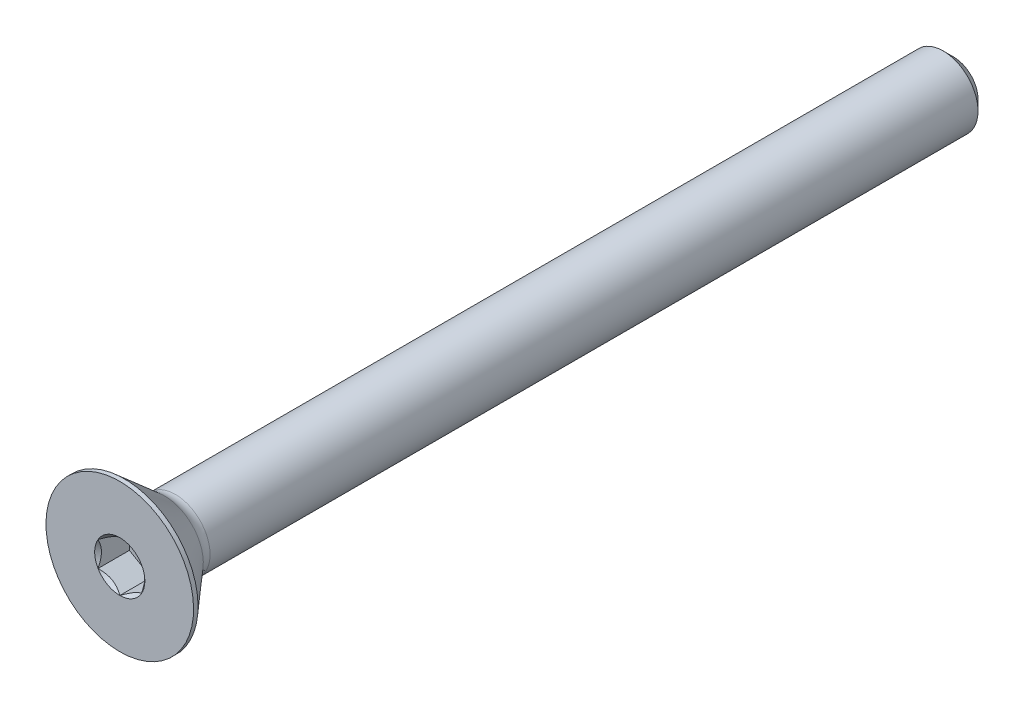
SolidWorks part; units mm, degrees
ref_plane "Front" through (0, 0, 0) normal (0, 0, 1) x (1, 0, 0)
ref_plane "Top" through (0, 0, 0) normal (0, 1, 0) x (1, 0, 0)
ref_plane "Right" through (0, 0, 0) normal (1, 0, 0) x (0, 0, -1)
sketch "Sketch1" plane through (0, 0, 0) normal (1, 0, 0) x (0, 0, -1)
  line L0 (0, 6.7437) -> (0.4089, 6.7437) construction
  line L1 (0.4089, 6.7437) -> (4.0894, 3.5443) construction
  line L2 (0, 3.175) -> (76.2, 3.175)
  line L3 (76.2, 3.175) -> (76.2, 0)
  line L4 (76.2, 0) -> (0, 0)
  line L5 (0, 0) -> (0, 6.7437) construction
  line L6 (0, 6.7437) -> (0, -6.7437) construction
  line L7 (76.2, 3.175) -> (76.2, -3.175) construction
  line L8 (0, -6.7437) -> (0.4089, -6.7437) construction
  line L9 (0.4089, -6.7437) -> (4.0894, -3.5443) construction
  line L11 (0, 3.175) -> (0, 0)
  line L12 (5.0772, 3.175) -> (5.0772, 0) construction
  arc A1 (4.0894, 3.5443) -> (5.0772, 3.175) centre (5.0772, 4.6807) ccw construction
  dimension "D1" = 0.4089
revolve "Revolve1" add sketch "Sketch1" angle 360 mid plane about L4
sketch "Sketch3" plane through (0, 0, -76.2) normal (0, 0, -1) x (-1, 0, 0)
  circle A0 centre (0, 0) radius 3.175
curve "Helix/Spiral1" pitch 1.27 height 76.2 turns 60
sketch "Sketch2" plane through (0, 0, 0) normal (1, 0, 0) x (0, 0, -1)
  line L0 (76.2, 3.175) -> (77.3113, 3.175)
  line L1 (77.3113, 3.175) -> (76.835, 2.3501)
  line L2 (76.835, 2.3501) -> (76.6762, 2.3501)
  line L3 (76.6762, 2.3501) -> (76.2, 3.175)
  line L4 (76.4381, 2.7626) -> (77.0731, 2.7626) construction
  dimension "D1" = 60
  dimension "D2" = 0.1588
  dimension "D3" = 0.635
chamfer "Chamfer1" distance 0.9525 angle 45 1 edges at (0, 3.175, -76.2)
sketch "Sketch7" plane through (0, 0, 0) normal (1, 0, 0) x (0, 0, -1)
  line L0 (0, 6.7437) -> (0.4089, 6.7437) construction
  line L1 (0.4089, 6.7437) -> (4.0894, 3.5443) construction
  line L2 (0, 6.7437) -> (0.4089, 6.7437)
  line L3 (0.4089, 6.7437) -> (4.0894, 3.5443)
  line L4 (5.0772, 3.175) -> (5.0772, 0) construction
  line L5 (5.0772, 3.175) -> (5.0772, 0)
  line L7 (0, 0) -> (0, 6.7437) construction
  line L8 (0, 0) -> (0, 6.7437)
  line L9 (0, 0) -> (5.0772, 0)
  line L10 (7.4181, 0) -> (-7.4181, 0) construction
  arc A0 (4.0894, 3.5443) -> (5.0772, 3.175) centre (5.0772, 4.6807) ccw construction
  arc A1 (4.0894, 3.5443) -> (5.0772, 3.175) centre (5.0772, 4.6807) ccw
revolve "Revolve2" add sketch "Sketch7" angle 360 mid plane about L9
ref_plane "Plane1" through (0, 0, -5.0772) normal (0, 0, 1) x (1, 0, 0)
sketch "Sketch8" plane through (0, 0, -5.0772) normal (0, 0, 1) x (1, 0, 0)
  circle A0 centre (0, 0) radius 3.175
extrude "Boss-Extrude1" add sketch "Sketch8" against normal through all draft 45
sketch "Sketch5" plane through (0, 0, 0) normal (0, 0, 1) x (1, 0, 0)
  line L1 (1.9844, -1.1457) -> (1.9844, 1.1457)
  line L2 (1.9844, 1.1457) -> (0, 2.2914)
  line L3 (0, 2.2914) -> (-1.9844, 1.1457)
  line L4 (-1.9844, 1.1457) -> (-1.9844, -1.1457)
  line L5 (-1.9844, -1.1457) -> (0, -2.2914)
  line L6 (0, -2.2914) -> (1.9844, -1.1457)
  circle A0 centre (0, 0) radius 1.9844 construction
  dimension "Hex" = 3.9688
extrude "Cut-Extrude2" cut sketch "Sketch5" against normal blind 2.8626
sketch "Sketch6" plane through (0, 0, 0) normal (0, 0, 1) x (1, 0, 0)
  circle A0 centre (0, 0) radius 2.2914
extrude "Cut-Extrude3" cut sketch "Sketch6" against normal through all draft 45
sketch "Sketch9" plane through (0, 0, -5.0772) normal (0, 0, 1) x (1, 0, 0)
  circle A1 centre (0, 0) radius 3.175
  circle A2 centre (0, 0) radius 3.175
  point P0 (0, 3.175)
  dimension "D1" = 0
extrude "Boss-Extrude2" add sketch "Sketch9" against normal offset from surface (45.7228 mm away) 25.4 up to face at (0, 2.2225, -76.2)
sketch "Sketch10" plane through (0, 0, 0) normal (1, 0, 0) x (0, 0, -1)
  line L0 (76.2, 3.175) -> (76.2, -3.175) construction
  point P0 (74.295, -3.175)
  dimension "D1" = 1.905
equation "\"D3@Helix/Spiral1\" = \"Lg@Sketch1\""
equation "\"D2@Sketch2\" = \"D4@Helix/Spiral1\" * .125"
equation "\"D3@Sketch2\" = \"D4@Helix/Spiral1\" * .5"
equation "\"D1@Chamfer1\" = \"D4@Helix/Spiral1\" * .75"
equation "\"D1@Cut-Extrude2\" = \"Head Ht@Sketch1\" * .7"
equation "\"D1@Sketch1\" = \"Head Ht@Sketch1\" * .1"
equation "\"D1@Sketch10\" = \"D4@Helix/Spiral1\" * 1.5"
